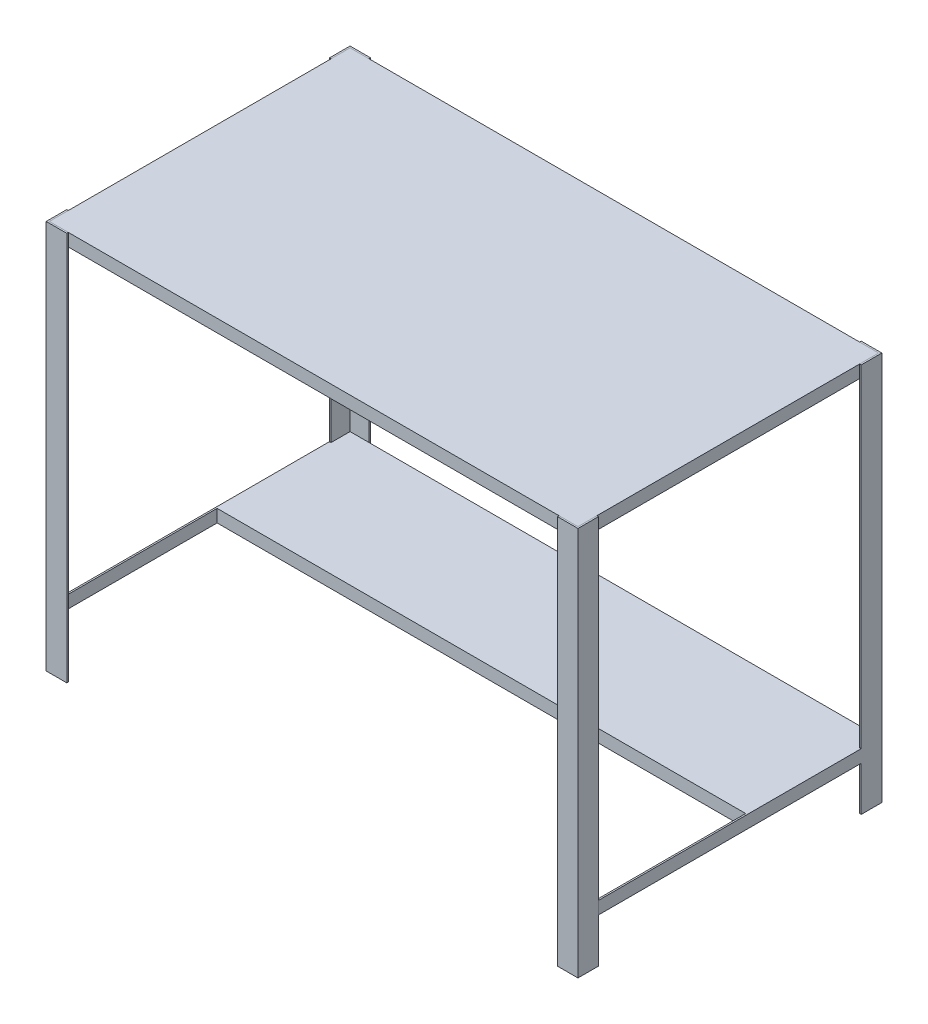
SolidWorks part; units mm, degrees
ref_plane "Front Plane" through (0, 0, 0) normal (0, 0, 1) x (1, 0, 0)
ref_plane "Top Plane" through (0, 0, 0) normal (0, 1, 0) x (1, 0, 0)
ref_plane "Right Plane" through (0, 0, 0) normal (1, 0, 0) x (0, 0, -1)
sketch "Sketch1" plane through (0, 0, 0) normal (0, 1, 0) x (1, 0, 0)
  line L1 (-530.225, -301.625) -> (530.225, -301.625)
  line L2 (-530.225, -301.625) -> (-530.225, 301.625)
  line L3 (-530.225, 301.625) -> (530.225, 301.625)
  line L4 (530.225, -301.625) -> (530.225, 301.625)
  point P4 (0, 301.625)
  point P6 (-530.225, 0)
  dimension "D1" = 603.25
  dimension "D2" = 1060.45
extrude "Boss-Extrude1" add sketch "Sketch1" along normal blind 25.4
sketch "Sketch2" plane through (0, 0, 0) normal (0, -1, 0) x (-1, 0, 0)
  line L0 (0, -375.7222) -> (0, 398.6255) construction
  line L1 (665.2847, 0) -> (-691.4598, 0) construction
  line L2 (492.125, -301.625) -> (492.125, -304.8)
  line L4 (492.125, -304.8) -> (533.4, -304.8)
  line L5 (533.4, -304.8) -> (533.4, -263.525)
  line L6 (533.4, -263.525) -> (530.225, -263.525)
  line L7 (530.225, 301.625) -> (530.225, -301.625) construction
  line L8 (530.225, -263.525) -> (530.225, -301.625)
  line L9 (530.225, -301.625) -> (492.125, -301.625)
  line L10 (530.225, -301.625) -> (-530.225, -301.625) construction
  line L11 (-530.225, -301.625) -> (-492.125, -301.625)
  line L12 (-530.225, -263.525) -> (-530.225, -301.625)
  line L13 (-533.4, -263.525) -> (-530.225, -263.525)
  line L14 (-533.4, -304.8) -> (-533.4, -263.525)
  line L15 (-492.125, -304.8) -> (-533.4, -304.8)
  line L16 (-492.125, -301.625) -> (-492.125, -304.8)
  line L17 (-492.125, 301.625) -> (-492.125, 304.8)
  line L18 (-492.125, 304.8) -> (-533.4, 304.8)
  line L19 (-533.4, 304.8) -> (-533.4, 263.525)
  line L20 (-533.4, 263.525) -> (-530.225, 263.525)
  line L21 (-530.225, 263.525) -> (-530.225, 301.625)
  line L22 (-530.225, 301.625) -> (-492.125, 301.625)
  line L23 (530.225, 301.625) -> (492.125, 301.625)
  line L24 (530.225, 263.525) -> (530.225, 301.625)
  line L25 (533.4, 263.525) -> (530.225, 263.525)
  line L26 (533.4, 304.8) -> (533.4, 263.525)
  line L27 (492.125, 304.8) -> (533.4, 304.8)
  line L28 (492.125, 301.625) -> (492.125, 304.8)
  point P10 (0, 0)
  dimension "D1" = 3.175
  dimension "D2" = 3.175
  dimension "D3" = 38.1
  dimension "D4" = 38.1
extrude "Boss-Extrude2" add sketch "Sketch2" along normal blind 755.65 and the other way up to surface (25.4 mm away) separate body other way up to face at (0, 25.4, 0)
sketch "Sketch3" plane through (530.225, 0, 0) normal (-1, 0, 0) x (0, 0, 1)
  line L1 (-301.625, -641.35) -> (-34.925, -641.35)
  line L2 (-301.625, -641.35) -> (-301.625, -666.75)
  line L3 (-301.625, -666.75) -> (-34.925, -666.75)
  line L4 (-34.925, -641.35) -> (-34.925, -666.75)
  line L5 (301.625, -755.65) -> (263.525, -755.65) construction
  line L6 (-301.625, 25.4) -> (-301.625, -755.65) construction
  dimension "D1" = 25.4
  dimension "D2" = 266.7
  dimension "D3" = 88.9
extrude "Boss-Extrude3" add sketch "Sketch3" along normal up to surface (1060.45 mm away) up to face at (-530.225, -365.125, 282.575)
sketch "Sketch4" plane through (0, 0, -263.525) normal (0, 0, -1) x (-1, 0, 0)
  line L0 (533.4, 25.4) -> (533.4, -755.65) construction
  line L1 (533.4, -666.75) -> (530.225, -666.75)
  line L2 (533.4, -666.75) -> (533.4, -641.35)
  line L3 (533.4, -641.35) -> (530.225, -641.35)
  line L4 (530.225, -666.75) -> (530.225, -641.35)
  line L6 (530.225, -641.35) -> (-530.225, -641.35) construction
  line L7 (530.225, -666.75) -> (-530.225, -666.75) construction
  point P4 (0, 0)
  point P5 (0, 0)
  point P10 (0, 0)
  point P11 (0, 0)
  point P12 (0, 0)
  point P18 (0, 0)
extrude "Boss-Extrude4" add sketch "Sketch4" against normal up to surface (527.05 mm away) up to face at (-531.8125, -365.125, 263.525)
mirror "Mirror2" about plane through (0, 0, 0) normal (1, 0, 0) of "Boss-Extrude4"
